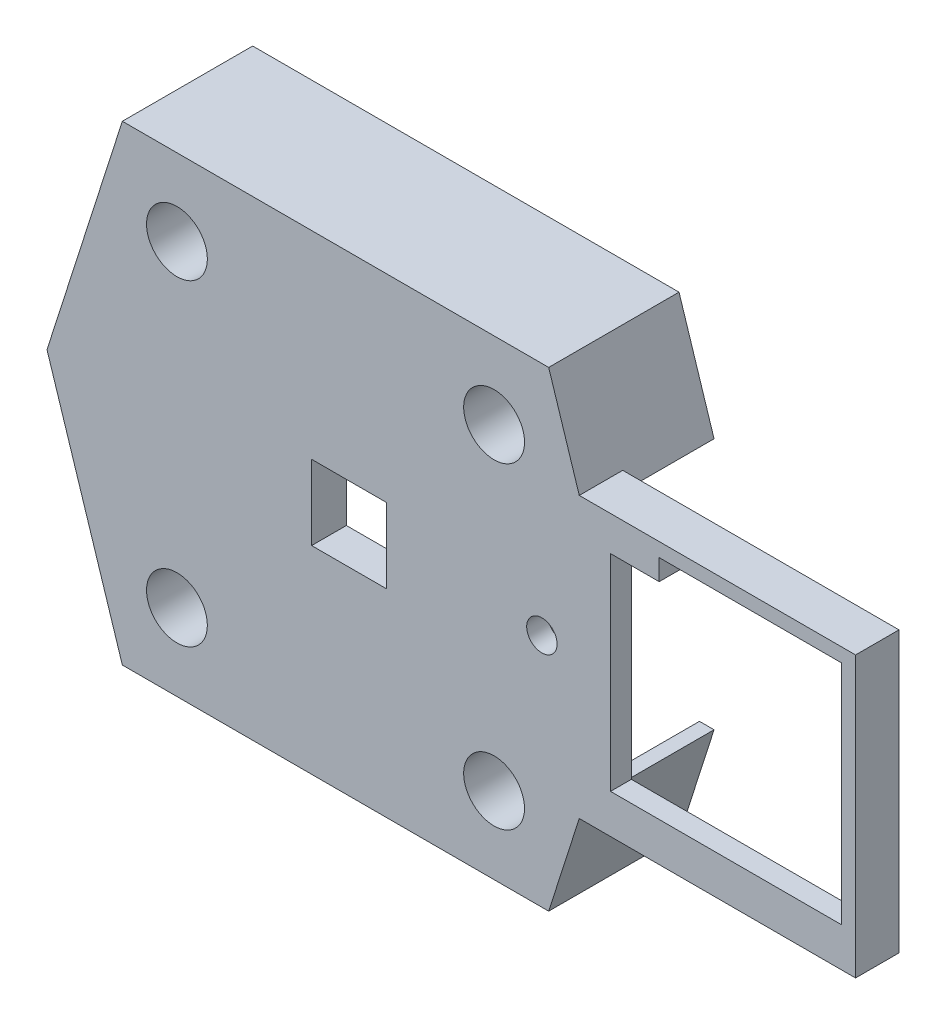
SolidWorks part; units mm, degrees
ref_plane "Front Plane" through (0, 0, 0) normal (0, 0, 1) x (1, 0, 0)
ref_plane "Top Plane" through (0, 0, 0) normal (0, 1, 0) x (1, 0, 0)
ref_plane "Right Plane" through (0, 0, 0) normal (1, 0, 0) x (0, 0, -1)
sketch "Sketch2" plane through (0, 0, 12) normal (0, 0, 1) x (1, 0, 0)
  line L10 (-24.5329, 27.1) -> (-33.2049, 0)
  line L11 (-33.2049, 0) -> (-24.5329, -27.1)
  line L12 (-24.5329, -27.1) -> (24.5329, -27.1)
  line L13 (24.5329, -27.1) -> (33.2049, 0)
  line L14 (33.2049, 0) -> (24.5329, 27.1)
  line L15 (24.5329, 27.1) -> (-24.5329, 27.1)
  line L16 (-23.365, 25.5) -> (-31.525, 0)
  line L17 (-31.525, 0) -> (-23.365, -25.5)
  line L18 (-23.365, -25.5) -> (23.365, -25.5)
  line L19 (23.365, -25.5) -> (31.525, 0)
  line L20 (31.525, 0) -> (23.365, 25.5)
  line L21 (23.365, 25.5) -> (-23.365, 25.5)
  line L22 (-23.365, 25.5) -> (-31.525, 0)
  line L23 (-31.525, 0) -> (-23.365, -25.5)
  line L24 (-23.365, -25.5) -> (23.365, -25.5)
  line L25 (23.365, -25.5) -> (31.525, 0)
  line L26 (31.525, 0) -> (23.365, 25.5)
  line L27 (23.365, 25.5) -> (-23.365, 25.5)
  dimension "D1" = 0.5
  dimension "D2" = 1.6
extrude "Boss-Extrude1" add sketch "Sketch2" along normal blind 10 and the other way blind 5
sketch "Sketch3" plane through (0, 0, 22) normal (0, 0, 1) x (1, 0, 0)
  line L0 (29.75, 16.1) -> (59.85, 16.1)
  line L1 (59.85, 16.1) -> (59.85, -16.1)
  line L2 (59.85, -16.1) -> (29.75, -16.1)
  line L3 (29.75, 16.1) -> (28.0529, 16.1)
  line L4 (28.0529, 16.1) -> (28.5649, 14.5)
  line L5 (29.75, -16.1) -> (28.0529, -16.1)
  line L6 (28.0529, -16.1) -> (28.5649, -14.5)
  line L12 (29.75, 14.5) -> (28.5649, 14.5)
  line L13 (33.2049, 0) -> (24.5329, 27.1) construction
  line L14 (29.75, -14.5) -> (28.5649, -14.5)
  line L15 (58.25, -14.5) -> (29.75, -14.5)
  line L16 (58.25, 14.5) -> (58.25, -14.5)
  line L17 (29.75, 14.5) -> (58.25, 14.5)
  line L18 (58.25, -14.5) -> (29.75, -14.5)
  line L19 (58.25, 14.5) -> (58.25, -14.5)
  line L20 (29.75, 14.5) -> (58.25, 14.5)
  line L21 (24.5329, -27.1) -> (33.2049, 0) construction
  dimension "D1" = 0.5
  dimension "D2" = 1.6
extrude "Boss-Extrude2" add sketch "Sketch3" against normal blind 5
sketch "Sketch4" plane through (0, 0, 7) normal (0, 0, -1) x (-1, 0, 0)
  line L0 (-28.5649, 14.5) -> (-26.885, 14.5)
  line L1 (-31.525, 0) -> (-23.365, 25.5) construction
  line L2 (-28.5649, -14.5) -> (-26.885, -14.5)
  line L3 (-23.365, -25.5) -> (-31.525, 0) construction
  line L6 (24.5329, 27.1) -> (-24.5329, 27.1)
  line L7 (-24.5329, 27.1) -> (-33.2049, 0)
  line L8 (-33.2049, 0) -> (-24.5329, -27.1)
  line L9 (-24.5329, -27.1) -> (24.5329, -27.1)
  line L10 (24.5329, -27.1) -> (33.2049, 0)
  line L11 (33.2049, 0) -> (24.5329, 27.1)
  line L12 (24.5329, 27.1) -> (-24.5329, 27.1)
  line L13 (-24.5329, 27.1) -> (-33.2049, 0)
  line L14 (-33.2049, 0) -> (-24.5329, -27.1)
  line L15 (-24.5329, -27.1) -> (24.5329, -27.1)
  line L16 (24.5329, -27.1) -> (33.2049, 0)
  line L17 (33.2049, 0) -> (24.5329, 27.1)
  line M7 (-31.525, 0) -> (-23.365, 25.5)
  line M12 (-23.365, -25.5) -> (-31.525, 0)
  line M14 (-24.5329, 27.1) -> (-33.2049, 0)
  line M15 (-33.2049, 0) -> (-24.5329, -27.1)
  dimension "D1" = 0
extrude "Cut-Extrude1" cut sketch "Sketch4" against normal through all contours L2 L0 M15 M12 M7 M14
sketch "Sketch5" plane through (0, 0, 22) normal (0, 0, 1) x (1, 0, 0)
  line L0 (-2.25, 3.8) -> (-2.25, -3.8) construction
  line L1 (-2.25, -3.8) -> (29.75, -3.8) construction
  line L2 (29.75, -3.8) -> (29.75, -14) construction
  line L3 (29.75, -14) -> (57.75, -14) construction
  line L4 (57.75, -14) -> (57.75, 14) construction
  line L5 (57.75, 14) -> (29.75, 14) construction
  line L6 (29.75, 14) -> (29.75, 3.8) construction
  line L7 (29.75, 3.8) -> (-2.25, 3.8) construction
  line L8 (24.5329, -27.1) -> (28.0529, -16.1) construction
  line L9 (28.0529, -16.1) -> (59.85, -16.1) construction
  line L10 (59.85, -16.1) -> (59.85, 16.1) construction
  line L11 (59.85, 16.1) -> (28.0529, 16.1) construction
  line L12 (28.0529, 16.1) -> (24.5329, 27.1) construction
  line L13 (24.5329, 27.1) -> (-24.5329, 27.1) construction
  line L14 (-24.5329, 27.1) -> (-33.2049, 0) construction
  line L15 (-33.2049, 0) -> (-24.5329, -27.1) construction
  line L16 (-24.5329, -27.1) -> (24.5329, -27.1) construction
  line L17 (-2.25, 3.8) -> (-2.25, -3.8)
  line L18 (-2.25, -3.8) -> (29.75, -3.8)
  line L19 (29.75, -3.8) -> (29.75, -14)
  line L20 (29.75, -14) -> (57.75, -14)
  line L21 (57.75, -14) -> (57.75, 14)
  line L22 (57.75, 14) -> (29.75, 14)
  line L23 (29.75, 14) -> (29.75, 3.8)
  line L24 (29.75, 3.8) -> (-2.25, 3.8)
  line L25 (24.5329, -27.1) -> (28.0529, -16.1)
  line L26 (28.0529, -16.1) -> (59.85, -16.1)
  line L27 (59.85, -16.1) -> (59.85, 16.1)
  line L28 (59.85, 16.1) -> (28.0529, 16.1)
  line L29 (28.0529, 16.1) -> (24.5329, 27.1)
  line L30 (24.5329, 27.1) -> (-24.5329, 27.1)
  line L31 (-24.5329, 27.1) -> (-33.2049, 0)
  line L32 (-33.2049, 0) -> (-24.5329, -27.1)
  line L33 (-24.5329, -27.1) -> (24.5329, -27.1)
  line L34 (29.25, 14) -> (29.25, 4.3)
  line L35 (29.25, 4.3) -> (-2.75, 4.3)
  line L36 (-2.75, 4.3) -> (-2.75, -4.3)
  line L37 (-2.75, -4.3) -> (29.25, -4.3)
  line L38 (29.25, -4.3) -> (29.25, -14)
  line L39 (29.25, 14) -> (29.25, 14.5)
  line L40 (26.885, 14.5) -> (58.25, 14.5) construction
  line L41 (29.25, -14) -> (29.25, -14.5)
  line L42 (58.25, -14.5) -> (26.885, -14.5) construction
  line L43 (27.65, 14) -> (27.65, 14.5)
  line L44 (27.65, 14) -> (27.65, 5.9)
  line L45 (27.65, 5.9) -> (-4.35, 5.9)
  line L46 (-4.35, 5.9) -> (-4.35, -5.9)
  line L47 (-4.35, -5.9) -> (27.65, -5.9)
  line L48 (27.65, -5.9) -> (27.65, -14)
  line L49 (27.65, -14) -> (27.65, -14.5)
  circle A0 centre (18.25, -18.25) radius 3.5 construction
  circle A1 centre (-18.25, -18.25) radius 3.5 construction
  circle A2 centre (-18.25, 18.25) radius 3.5 construction
  circle A3 centre (18.25, 18.25) radius 3.5 construction
  circle A4 centre (18.25, -18.25) radius 3.5
  circle A5 centre (-18.25, -18.25) radius 3.5
  circle A6 centre (-18.25, 18.25) radius 3.5
  circle A7 centre (18.25, 18.25) radius 3.5
  line M28 (26.885, 14.5) -> (58.25, 14.5)
  line M30 (58.25, -14.5) -> (26.885, -14.5)
  dimension "D1" = 0.5
  dimension "D2" = 1.6
extrude "Boss-Extrude3" add sketch "Sketch5" against normal blind 4 contours L48 L49 L41 L38 L37 L36 L35 L34 L39 L43 L44 L45 L46 L47 M30 M28
sketch "Sketch7" plane through (0, 0, 22) normal (0, 0, 1) x (1, 0, 0)
  line L5 (37.25, 14.5) -> (37.25, 12.1)
  line L6 (29.25, 14.5) -> (58.25, 14.5) construction
  line L7 (37.25, 12.1) -> (31.65, 12.1)
  line L8 (31.65, 12.1) -> (31.65, -11.6)
  line L9 (31.65, -11.6) -> (58.25, -11.6)
  line L10 (58.25, 14.5) -> (58.25, -14.5) construction
  line L11 (5.85, 4.3) -> (5.85, -4.3)
  line L12 (29.25, 4.3) -> (-2.75, 4.3) construction
  line L13 (-2.75, -4.3) -> (29.25, -4.3) construction
  line L14 (29.25, 14.5) -> (29.25, 4.3) construction
  line L15 (-2.75, 4.3) -> (-2.75, -4.3) construction
  line L16 (29.75, -14) -> (57.75, -14) construction
  circle A0 centre (23.75, 0) radius 1.75 construction
  circle A1 centre (23.75, 0) radius 1.75
  line M29 (58.25, -14.5) -> (29.25, -14.5)
  line M30 (29.25, -14.5) -> (29.25, -4.3)
  line M31 (29.25, -4.3) -> (-2.75, -4.3)
  line M33 (-2.75, 4.3) -> (29.25, 4.3)
  line M34 (29.25, 4.3) -> (29.25, 14.5)
  line M35 (29.25, 14.5) -> (58.25, 14.5)
  line M36 (58.25, 14.5) -> (58.25, -14.5)
  dimension "D1" = 8.6
  dimension "D2" = 2.4
  dimension "D3" = 2.4
  dimension "D4" = 2.4
  dimension "D5" = 8
extrude "Boss-Extrude4" add sketch "Sketch7" against normal blind 2.4 contours L11 L9 L8 L7 L5 A1 M33 M31 M30 M29 M36 M35 M34
sketch "Sketch8" plane through (0, 0, 22) normal (0, 0, 1) x (1, 0, 0)
  circle A0 centre (-18.25, -18.25) radius 3.5 construction
  circle A1 centre (18.25, -18.25) radius 3.5 construction
  circle A2 centre (18.25, 18.25) radius 3.5 construction
  circle A3 centre (-18.25, 18.25) radius 3.5 construction
  circle A4 centre (-18.25, -18.25) radius 3.5
  circle A5 centre (18.25, -18.25) radius 3.5
  circle A6 centre (18.25, 18.25) radius 3.5
  circle A7 centre (-18.25, 18.25) radius 3.5
  line M11 (27.65, -5.9) -> (27.65, -14.5)
  line M12 (27.65, -14.5) -> (26.885, -14.5)
  line M13 (26.885, -14.5) -> (23.365, -25.5)
  line M14 (23.365, -25.5) -> (-23.365, -25.5)
  line M15 (-23.365, -25.5) -> (-31.525, 0)
  line M16 (-31.525, 0) -> (-23.365, 25.5)
  line M17 (-23.365, 25.5) -> (23.365, 25.5)
  line M18 (23.365, 25.5) -> (26.885, 14.5)
  line M19 (26.885, 14.5) -> (27.65, 14.5)
  line M20 (27.65, 14.5) -> (27.65, 5.9)
  line M21 (27.65, 5.9) -> (-4.35, 5.9)
  line M22 (-4.35, 5.9) -> (-4.35, -5.9)
  line M23 (-4.35, -5.9) -> (27.65, -5.9)
extrude "Boss-Extrude5" add sketch "Sketch8" against normal blind 1 contours A7 A6 A5 A4 M11 M23 M22 M21 M20 M19 M18 M17 M16 M15 M14 M13 M12
sketch "Sketch9" plane through (0, 0, 21) normal (0, 0, -1) x (-1, 0, 0)
  circle A0 centre (-18.25, -18.25) radius 3.5 construction
  circle A1 centre (18.25, -18.25) radius 3.5 construction
  circle A2 centre (18.25, 18.25) radius 3.5 construction
  circle A3 centre (-18.25, 18.25) radius 3.5 construction
  circle A4 centre (-18.25, -18.25) radius 3.5
  circle A5 centre (18.25, -18.25) radius 3.5
  circle A6 centre (18.25, 18.25) radius 3.5
  circle A7 centre (-18.25, 18.25) radius 3.5
  circle A8 centre (-18.25, 18.25) radius 5.1
  circle A9 centre (18.25, 18.25) radius 5.1
  circle A10 centre (18.25, -18.25) radius 5.1
  circle A11 centre (-18.25, -18.25) radius 5.1
  dimension "D1" = 1.6
extrude "Boss-Extrude6" add sketch "Sketch9" along normal blind 9
